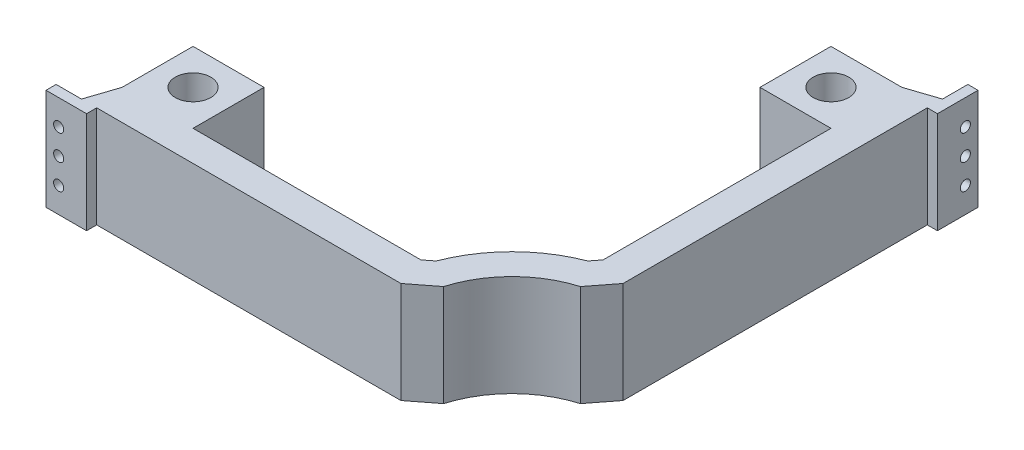
SolidWorks part; units mm, degrees
ref_plane "Front Plane" through (0, 0, 0) normal (0, 0, 1) x (1, 0, 0)
ref_plane "Top Plane" through (0, 0, 0) normal (0, 1, 0) x (1, 0, 0)
ref_plane "Right Plane" through (0, 0, 0) normal (1, 0, 0) x (0, 0, -1)
sketch "Sketch2" plane through (0, 0, 0) normal (0, 1, 0) x (1, 0, 0)
  line L0 (47.6057, -102.775) -> (59.4531, -93.5751)
  line L2 (102.3943, -47.9864) -> (93.1944, -59.8338)
  line L11 (107.3943, -107.775) -> (-5.1294, -107.775) construction
  line L15 (107.3943, -107.775) -> (107.3943, 82.0136) construction
  line L18 (47.6057, -102.775) -> (-54.8742, -102.775)
  line L19 (102.3943, 56.695) -> (102.3943, -47.9864)
  line L21 (87.3943, -42.8463) -> (84.0957, -47.0941)
  line L22 (42.4656, -87.775) -> (46.7134, -84.4764)
  line L24 (-102.3943, -102.775) -> (-54.8742, -102.775)
  line L25 (102.3943, 102.0136) -> (102.3943, 56.695)
  line L41 (102.3943, 102.0136) -> (107.3943, 102.0136)
  line L42 (107.3943, 102.0136) -> (107.3943, 122.0136)
  line L43 (107.3943, 122.0136) -> (102.3943, 122.0136)
  line L44 (102.3943, 122.0136) -> (102.3943, 109.5136)
  line L46 (52.3943, 104.5136) -> (52.3943, 69.5136)
  line L47 (52.3943, 69.5136) -> (87.3943, 69.5136)
  line L48 (87.3943, 69.5136) -> (87.3943, -42.8463)
  line L49 (-102.3943, -102.775) -> (-102.3943, -107.775)
  line L50 (-102.3943, -107.775) -> (-122.3943, -107.775)
  line L51 (-122.3943, -107.775) -> (-122.3943, -102.775)
  line L52 (-122.3943, -102.775) -> (-109.8943, -102.775)
  line L54 (-104.8943, -52.775) -> (-69.8943, -52.775)
  line L55 (-69.8943, -52.775) -> (-69.8943, -87.775)
  line L56 (-69.8943, -87.775) -> (42.4656, -87.775)
  line L57 (-104.8943, -52.775) -> (-104.8943, -87.775)
  line L58 (-104.8943, -87.775) -> (-109.8943, -102.775)
  line L59 (52.3943, 104.5136) -> (87.3943, 104.5136)
  line L60 (87.3943, 104.5136) -> (102.3943, 109.5136)
  arc A0 (93.1944, -59.8338) -> (59.4531, -93.5751) centre (107.3943, -107.775) ccw
  arc A1 (84.0957, -47.0941) -> (46.7134, -84.4764) centre (107.3943, -107.775) ccw
  arc A2 (107.3943, -57.775) -> (59.4531, -93.5751) centre (107.3943, -107.775) ccw
  point P0 (57.5862, -103.3993)
  point P3 (103.0186, -57.9669)
  point P4 (0, 0)
  point P23 (0, 0)
  dimension "D5" = 100
  dimension "D27" = 15
  dimension "D1" = 10
  dimension "D2" = 10
  dimension "D3" = 10
  dimension "D4" = 10
  dimension "D6" = 20
  dimension "D7" = 20
  dimension "D8" = 5
  dimension "D9" = 5
  dimension "D10" = 150
  dimension "D11" = 150
  dimension "D12" = 5
  dimension "D13" = 5
  dimension "D14" = 15
  dimension "D15" = 15
  dimension "D16" = 5
  dimension "D17" = 152.148
  dimension "D18" = 12.5
  dimension "D19" = 35
  dimension "D20" = 12.5
  dimension "D21" = 35
  dimension "D22" = 35
  dimension "D23" = 15
  dimension "D24" = 15
  dimension "D25" = 15
  dimension "D26" = 15
  dimension "D28" = 35
extrude "Boss-Extrude1" add sketch "Sketch2" along normal blind 50
sketch "Sketch3" plane through (0, 50, 0) normal (0, 1, 0) x (1, 0, 0)
  line L0 (-104.8943, -70.275) -> (-69.8943, -70.275) construction
  line L18 (-104.8943, -52.775) -> (-104.8943, -87.775) construction
  line L21 (-69.8943, -52.775) -> (-69.8943, -87.775) construction
  line L22 (69.8943, 104.5136) -> (69.8943, 69.5136) construction
  line L23 (52.3943, 104.5136) -> (87.3943, 104.5136) construction
  line L24 (52.3943, 69.5136) -> (87.3943, 69.5136) construction
  circle A5 centre (-87.3943, -70.275) radius 8.75
  circle A6 centre (69.8943, 87.0136) radius 8.75
  point P16 (0, 0)
  point P17 (-87.3943, -70.275)
  point P18 (0, 0)
  point P19 (69.8943, 87.0136)
  dimension "D1" = 17.5
extrude "Cut-Extrude1" cut sketch "Sketch3" against normal blind 50
sketch "Sketch5" plane through (0, 0, 102.775) normal (0, 0, -1) x (-1, 0, 0)
  line L0 (116.1443, 50) -> (116.1443, 25) construction
  line L3 (116.1443, 25) -> (109.8943, 25) construction
  line L4 (109.8943, 50) -> (109.8943, 0) construction
  line L5 (122.3943, 50) -> (109.8943, 50) construction
  line L6 (116.1443, 25) -> (116.1443, 0) construction
  line L7 (102.3943, 0) -> (122.3943, 0) construction
  circle A0 centre (116.1443, 37.5) radius 2.5
  circle A1 centre (116.1443, 25) radius 2.5
  circle A2 centre (116.1443, 12.5) radius 2.5
  dimension "D1" = 5
extrude "Cut-Extrude3" cut sketch "Sketch5" against normal blind 10
sketch "Sketch6" plane through (102.3943, 0, 0) normal (-1, 0, 0) x (0, 0, 1)
  line L0 (-115.7636, 50) -> (-115.7636, 25) construction
  line L3 (-115.7636, 25) -> (-109.5136, 25) construction
  line L4 (-109.5136, 50) -> (-109.5136, 0) construction
  line L5 (-122.0136, 50) -> (-109.5136, 50) construction
  line L6 (-115.7636, 25) -> (-115.7636, 0) construction
  line L7 (-102.0136, 0) -> (-122.0136, 0) construction
  circle A0 centre (-115.7636, 37.5) radius 2.5
  circle A1 centre (-115.7636, 25) radius 2.5
  circle A2 centre (-115.7636, 12.5) radius 2.5
  dimension "D1" = 5
extrude "Cut-Extrude4" cut sketch "Sketch6" against normal blind 10
